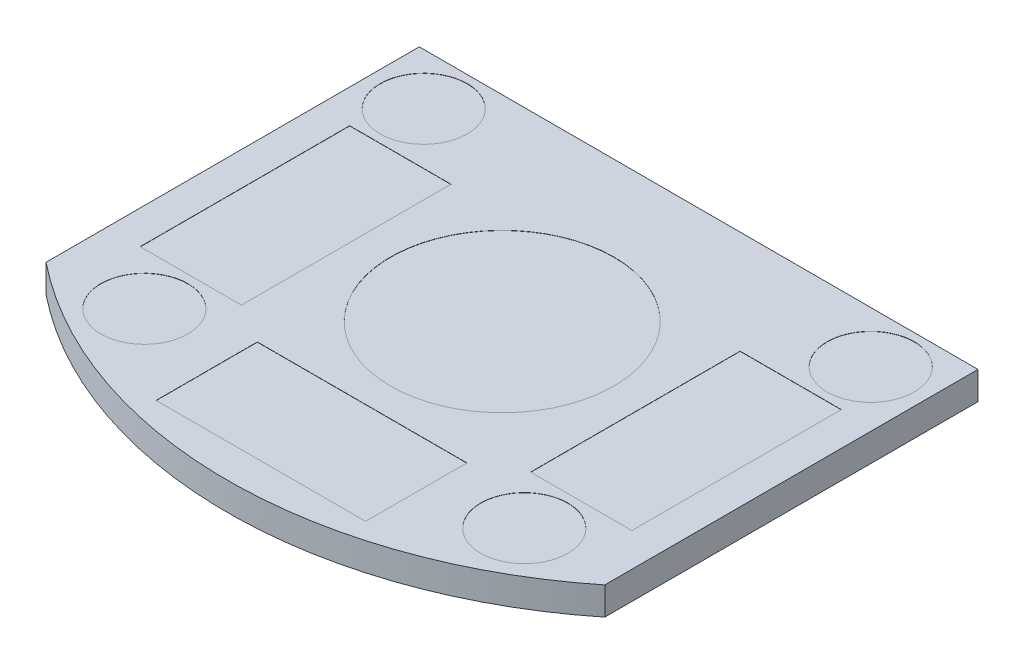
SolidWorks part; units mm, degrees
material "Silicon Rubber"
ref_plane "Front Plane" through (0, 0, 0) normal (0, 0, 1) x (1, 0, 0)
ref_plane "Top Plane" through (0, 0, 0) normal (0, 1, 0) x (1, 0, 0)
ref_plane "Right Plane" through (0, 0, 0) normal (1, 0, 0) x (0, 0, -1)
sketch "Sketch1" plane through (0, 0, 0) normal (0, 1, 0) x (1, 0, 0)
  line L1 (-31.75, 0) -> (31.75, 0)
  line L2 (-31.75, 0) -> (-31.75, -42.418)
  line L4 (31.75, 0) -> (31.75, -42.418)
  arc A0 (-31.75, -42.418) -> (31.75, -42.418) centre (0, -2.7623) ccw
  point P4 (0, 0)
  dimension "D3" = 50.8
  dimension "D1" = 63.5
  dimension "D2" = 42.418
extrude "Boss-Extrude1" add sketch "Sketch1" along normal blind 12.7
ref_plane "Plane1" through (-19.558, 0, 0) normal (-1, 0, 0) x (0, 0, 1)
sketch "Sketch2" plane through (-19.558, 0, 0) normal (-1, 0, 0) x (0, 0, 1)
  line L7 (0, 0) -> (0, 17.5687) construction
  line L9 (0, 0) -> (-12.7, 0)
  line L10 (0, 0) -> (0, 12.7)
  arc A2 (0, 12.7) -> (-12.7, 0) centre (-12.7, 12.7) ccw
  point P2 (-12.7, 0)
  point P3 (0, 12.7)
  dimension "D1" = 25.4
  dimension "D2" = 17.5687
extrude "Boss-Extrude2" add sketch "Sketch2" against normal blind 11.176
mirror "Mirror1" about plane through (0, 0, 0) normal (1, 0, 0) of "Boss-Extrude2"
sketch "Sketch20" plane through (0, 0, 0) normal (0, -1, 0) x (1, 0, 0)
  line L11 (-31.75, 42.418) -> (-31.75, 0)
  line L12 (-31.75, 0) -> (-19.558, 0)
  line L13 (-19.558, 0) -> (-19.558, -12.7)
  line L14 (-19.558, -12.7) -> (-8.382, -12.7)
  line L15 (-8.382, -12.7) -> (-8.382, 0)
  line L16 (-8.382, 0) -> (8.382, 0)
  line L17 (8.382, 0) -> (8.382, -12.7)
  line L18 (8.382, -12.7) -> (19.558, -12.7)
  line L19 (19.558, -12.7) -> (19.558, 0)
  line L20 (19.558, 0) -> (31.75, 0)
  line L21 (31.75, 0) -> (31.75, 42.418)
  line L22 (-31.75, 42.418) -> (-31.75, 0)
  line L23 (-31.75, 0) -> (-19.558, 0)
  line L24 (-19.558, 0) -> (-19.558, -12.7)
  line L25 (-19.558, -12.7) -> (-8.382, -12.7)
  line L26 (-8.382, -12.7) -> (-8.382, 0)
  line L27 (-8.382, 0) -> (8.382, 0)
  line L28 (8.382, 0) -> (8.382, -12.7)
  line L29 (8.382, -12.7) -> (19.558, -12.7)
  line L30 (19.558, -12.7) -> (19.558, 0)
  line L31 (19.558, 0) -> (31.75, 0)
  line L32 (31.75, 0) -> (31.75, 42.418)
  arc A1 (31.75, 42.418) -> (-31.75, 42.418) centre (0, 2.7623) ccw
  arc A2 (31.75, 42.418) -> (-31.75, 42.418) centre (0, 2.7623) ccw
  dimension "D1" = 0
extrude "Boss-Extrude10" add sketch "Sketch20" along normal blind 3.175
ref_plane "Plane3" through (0, 0, 0) normal (0, -1, 0) x (-1, 0, 0)
sketch "Sketch22" plane through (0, 0, 0) normal (0, -1, 0) x (-1, 0, 0)
  line L1 (-48.2287, -57.9234) -> (43.957, -57.9234)
  line L2 (-48.2287, -57.9234) -> (-48.2287, 31.5011)
  line L3 (-48.2287, 31.5011) -> (43.957, 31.5011)
  line L4 (43.957, -57.9234) -> (43.957, 31.5011)
extrude "Cut-Extrude13" cut sketch "Sketch22" against normal through all
sketch "Sketch26" plane through (0, 0, 0) normal (0, 1, 0) x (1, 0, 0)
  line L0 (8.382, 12.7) -> (19.558, 12.7) construction
  line L1 (-31.75, 0) -> (31.75, 0)
  line L2 (-31.75, 0) -> (-31.75, 12.7)
  line L3 (-31.75, 12.7) -> (31.75, 12.7)
  line L4 (31.75, 0) -> (31.75, 12.7)
  line L5 (31.75, -42.418) -> (31.75, 0) construction
extrude "Boss-Extrude11" add sketch "Sketch26" against normal up to surface (3.175 mm away) up to face at (0, -3.175, 3.765)
sketch "Sketch23" plane through (0, 0, 0) normal (0, 1, 0) x (1, 0, 0)
  line L0 (31.75, -42.418) -> (31.75, 12.7) construction
  line L1 (-21.59, -41.402) -> (-31.75, -41.402) construction
  line L2 (-31.75, 12.7) -> (-31.75, -42.418) construction
  line L3 (0, 0) -> (0, -53.5623) construction
  line L4 (31.75, 12.7) -> (-31.75, 12.7) construction
  line L5 (-25.4, -5.842) -> (-25.4, -41.402) construction
  circle A4 centre (25.4, -5.842) radius 4.953
  circle A5 centre (21.59, -41.402) radius 4.953
  circle A6 centre (-25.4, -5.842) radius 4.953
  circle A7 centre (-21.59, -41.402) radius 4.953
  circle A8 centre (0, -22.3203) radius 12.7
  arc A9 (-31.75, -42.418) -> (31.75, -42.418) centre (0, -2.7623) ccw construction
  point P4 (-25.4, -23.622)
  point P5 (0, -53.5623)
  point P16 (-31.75, -42.418)
  point P17 (31.75, 0)
  point P18 (-31.75, 0)
  point P19 (31.75, -42.418)
  dimension "D1" = 9.906
  dimension "D3" = 9.906
  dimension "D8" = 25.4
  dimension "D9" = 12.7
  dimension "D4" = 10.16
  dimension "D6" = 31.242
  dimension "D2" = 35.56
  dimension "D5" = 1.016
  dimension "D7" = 50.8
extrude "Cut-Extrude14" cut sketch "Sketch23" against normal blind 0.0254
sketch "Sketch25" plane through (0, 0, 0) normal (0, 1, 0) x (1, 0, 0)
  line L1 (-27.94, -11.7158) -> (-16.4306, -11.7158)
  line L2 (-27.94, -11.7158) -> (-27.94, -35.5283)
  line L3 (-25.4, -5.842) -> (25.4, -5.842) construction
  line L4 (-27.94, -35.5283) -> (-16.4306, -35.5283)
  line L5 (11.9063, -38.2429) -> (-11.9062, -38.2429)
  line L6 (11.9063, -38.2429) -> (11.9063, -49.7523)
  line L7 (11.9063, -49.7523) -> (-11.9062, -49.7523)
  line L8 (-11.9062, -38.2429) -> (-11.9062, -49.7523)
  line L9 (11.9063, -38.2429) -> (-11.9062, -49.7523) construction
  line L10 (11.9063, -49.7523) -> (-11.9062, -38.2429) construction
  line L15 (0, 0) -> (0, -53.5623) construction
  line L16 (16.4306, -11.7158) -> (16.4306, -35.5283)
  line L17 (-16.4306, -11.7158) -> (-16.4306, -35.5283)
  line L18 (-31.75, 12.7) -> (-31.75, -42.418) construction
  line L19 (27.94, -35.5283) -> (16.4306, -35.5283)
  line L20 (27.94, -11.7158) -> (27.94, -35.5283)
  line L21 (27.94, -11.7158) -> (16.4306, -11.7158)
  arc A0 (-31.75, -42.418) -> (31.75, -42.418) centre (0, -2.7623) ccw construction
  point P3 (-25.4, -5.842)
  point P5 (25.4, -5.842)
  point P26 (0, -53.5623)
  point P27 (0, -43.9976)
  dimension "D1" = 11.5094
  dimension "D2" = 23.8125
  dimension "D3" = 18.034
  dimension "D5" = 3.81
  dimension "D7" = 3.81
extrude "Cut-Extrude15" cut sketch "Sketch25" against normal blind 0.0254
sketch "Sketch27" plane through (0, 0, 0) normal (0, 1, 0) x (1, 0, 0)
  line L0 (-31.75, -42.418) -> (-31.75, 0) construction
  line L1 (-31.75, 12.7) -> (-31.75, -42.418) construction
  line L3 (-31.75, 0) -> (31.75, 0)
  line L4 (-31.75, 0) -> (-31.75, 12.7)
  line L5 (-31.75, 12.7) -> (31.75, 12.7)
  line L6 (31.75, 0) -> (31.75, 12.7)
extrude "Cut-Extrude16" cut sketch "Sketch27" against normal through all
